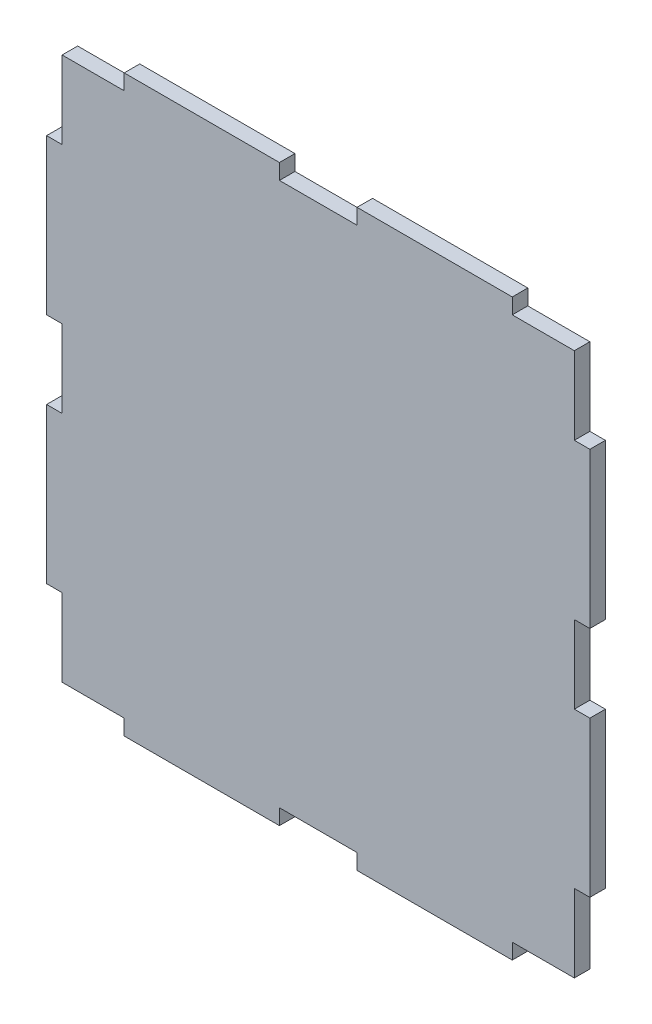
SolidWorks part; units mm, degrees
ref_plane "Front Plane" through (0, 0, 0) normal (0, 0, 1) x (1, 0, 0)
ref_plane "Top Plane" through (0, 0, 0) normal (0, 1, 0) x (1, 0, 0)
ref_plane "Right Plane" through (0, 0, 0) normal (1, 0, 0) x (0, 0, -1)
sketch "Sketch1" plane through (0, 0, 0) normal (0, 0, 1) x (1, 0, 0)
  line L1 (-33, -35) -> (33, -35)
  line L2 (-33, -35) -> (-33, 35)
  line L3 (-33, 35) -> (33, 35)
  line L4 (33, -35) -> (33, 35)
  line L5 (0, 35) -> (0, -35) construction
  line L6 (-33, 0) -> (33, 0) construction
  point P0 (0, 0)
  dimension "D1" = 66
  dimension "D2" = 70
extrude "Boss-Extrude1" add sketch "Sketch1" along normal blind 2
sketch "Sketch2" plane through (0, 0, 0) normal (0, 0, -1) x (-1, 0, 0)
  line L0 (-33, -35) -> (-33, 35) construction
  line L1 (-31, 5) -> (-35, 5)
  line L2 (-31, 5) -> (-31, -5)
  line L3 (-31, -5) -> (-35, -5)
  line L4 (-35, 5) -> (-35, -5)
  line L5 (-33, -5) -> (-33, 5) construction
  line L6 (-31, 0) -> (-35, 0) construction
  line L7 (-33, -35) -> (-33, 0)
  line L8 (-33, -5) -> (-35, -5)
  line L9 (-33, -5) -> (-33, -25)
  line L10 (-33, -25) -> (-35, -25)
  line L11 (-35, -5) -> (-35, -25)
  line L12 (-33, 5) -> (-35, 5)
  line L13 (-33, 5) -> (-33, 25)
  line L14 (-33, 25) -> (-35, 25)
  line L15 (-35, 5) -> (-35, 25)
  line L16 (35, 5) -> (31, 5)
  line L17 (35, 5) -> (35, -5)
  line L18 (35, -5) -> (31, -5)
  line L19 (31, 5) -> (31, -5)
  line L20 (33, -5) -> (33, 5) construction
  line L21 (35, 0) -> (31, 0) construction
  line L22 (33, -35) -> (33, 0)
  line L23 (33, -5) -> (31, -5)
  line L24 (33, -5) -> (33, -25)
  line L25 (33, -25) -> (31, -25)
  line L26 (31, -5) -> (31, -25)
  line L27 (33, 5) -> (31, 5)
  line L28 (33, 5) -> (33, 25)
  line L29 (33, 25) -> (31, 25)
  line L30 (31, 5) -> (31, 25)
  line L32 (33, -5) -> (35, -5)
  line L33 (33, -5) -> (33, -25)
  line L34 (33, -25) -> (35, -25)
  line L35 (35, -5) -> (35, -25)
  line L36 (35, 5) -> (33, 5)
  line L37 (35, 5) -> (35, 25)
  line L38 (35, 25) -> (33, 25)
  line L39 (33, 5) -> (33, 25)
  point P0 (-33, 0)
  point P12 (33, 0)
  line M5 (-33, 35) -> (-33, -35)
  line M7 (33, -35) -> (33, 35)
  dimension "D1" = 4
  dimension "D2" = 10
  dimension "D3" = 20
  dimension "D4" = 20
  dimension "D5" = 4
  dimension "D6" = 10
  dimension "D7" = 20
  dimension "D8" = 20
  dimension "D9" = 35
  dimension "D10" = 35
extrude "Boss-Extrude2" add sketch "Sketch2" against normal blind 2 contours L35 L18 L22 L34 | L37 L38 L16 M7 | L3 L11 L10 M5 | L15 L1 L14 M5
sketch "Sketch3" plane through (0, 0, 0) normal (0, 0, -1) x (-1, 0, 0)
  line L0 (-33, -35) -> (0, -35)
  line L1 (33, -35) -> (-33, -35) construction
  line L2 (-33, 35) -> (0, 35)
  line L3 (-5, -37) -> (5, -37)
  line L4 (-5, -37) -> (-5, -33)
  line L5 (-5, -33) -> (5, -33)
  line L6 (5, -37) -> (5, -33)
  line L7 (0, -33) -> (0, -37) construction
  line L8 (-5, -35) -> (5, -35) construction
  line L9 (5, -35) -> (25, -35)
  line L10 (5, -35) -> (5, -37)
  line L11 (5, -37) -> (25, -37)
  line L12 (25, -35) -> (25, -37)
  line L13 (-5, -35) -> (-25, -35)
  line L14 (-5, -35) -> (-5, -37)
  line L15 (-5, -37) -> (-25, -37)
  line L16 (-25, -35) -> (-25, -37)
  line L17 (-5, 33) -> (5, 33)
  line L18 (-5, 33) -> (-5, 37)
  line L19 (-5, 37) -> (5, 37)
  line L20 (5, 33) -> (5, 37)
  line L21 (0, 37) -> (0, 33) construction
  line L22 (-5, 35) -> (5, 35) construction
  line L23 (5, 35) -> (25, 35)
  line L24 (5, 35) -> (5, 33)
  line L25 (5, 33) -> (25, 33)
  line L26 (25, 35) -> (25, 33)
  line L27 (-5, 35) -> (-25, 35)
  line L28 (-5, 35) -> (-5, 33)
  line L29 (-5, 33) -> (-25, 33)
  line L30 (-25, 35) -> (-25, 33)
  line L32 (-25, 35) -> (-5, 35)
  line L33 (-25, 35) -> (-25, 37)
  line L34 (-25, 37) -> (-5, 37)
  line L35 (-5, 35) -> (-5, 37)
  line L36 (5, 35) -> (25, 35)
  line L37 (5, 35) -> (5, 37)
  line L38 (5, 37) -> (25, 37)
  line L39 (25, 35) -> (25, 37)
  line M6 (-33, -35) -> (33, -35)
  line M16 (33, 35) -> (-33, 35)
  dimension "D1" = 10
  dimension "D2" = 4
  dimension "D3" = 33
  dimension "D4" = 20
  dimension "D5" = 20
  dimension "D6" = 33
  dimension "D7" = 20
  dimension "D8" = 20
extrude "Boss-Extrude3" add sketch "Sketch3" against normal blind 2 contours L34 L33 L2 L18 | L39 L38 L20 M16 | L0 L16 L15 L4 | L12 L6 L11 M6
